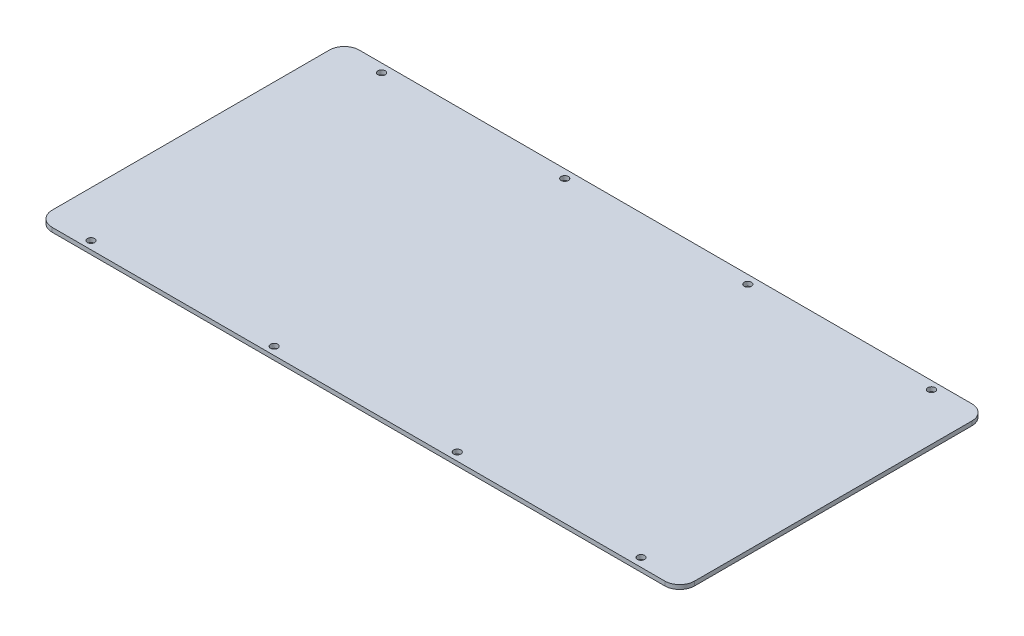
SolidWorks part; units mm, degrees
ref_plane "Front Plane" through (0, 0, 0) normal (0, 0, 1) x (1, 0, 0)
ref_plane "Top Plane" through (0, 0, 0) normal (0, 1, 0) x (1, 0, 0)
ref_plane "Right Plane" through (0, 0, 0) normal (1, 0, 0) x (0, 0, -1)
sketch "Sketch1" plane through (0, 0, 0) normal (0, 1, 0) x (1, 0, 0)
  line L1 (0, 0) -> (350, 0)
  line L2 (0, 0) -> (0, 250)
  line L3 (0, 250) -> (350, 250)
  line L4 (350, 0) -> (350, 250)
extrude "Boss-Extrude1" add sketch "Sketch1" along normal blind 2
sketch "Sketch4" plane through (0, 2, 0) normal (0, 1, 0) x (1, 0, 0)
  line L0 (26.4935, 73.7464) -> (26.4935, 203.9459)
  line L1 (321.1928, 66.7464) -> (33.4935, 66.7464)
  line L2 (328.1928, 203.9459) -> (328.1928, 73.7464)
  line L3 (33.4935, 210.9459) -> (321.1928, 210.9459)
  circle A0 centre (305.9935, 70.7464) radius 1.7
  circle A1 centre (219.9935, 70.4964) radius 1.7
  circle A2 centre (47.9935, 70.4964) radius 1.7
  circle A3 centre (133.9935, 70.4964) radius 1.7
  circle A4 centre (305.9935, 207.1959) radius 1.7
  circle A5 centre (219.9935, 206.9459) radius 1.7
  circle A6 centre (47.9935, 206.9459) radius 1.7
  circle A7 centre (133.9935, 206.9459) radius 1.7
  arc A8 (33.4935, 210.9459) -> (26.4935, 203.9459) centre (33.4935, 203.9459) ccw
  arc A9 (26.4935, 73.7464) -> (33.4935, 66.7464) centre (33.4935, 73.7464) ccw
  arc A10 (321.1928, 66.7464) -> (328.1928, 73.7464) centre (321.1928, 73.7464) ccw
  arc A11 (328.1928, 203.9459) -> (321.1928, 210.9459) centre (321.1928, 203.9459) ccw
extrude "Cut-Extrude1" cut sketch "Sketch4" against normal blind 2 flip side to cut
